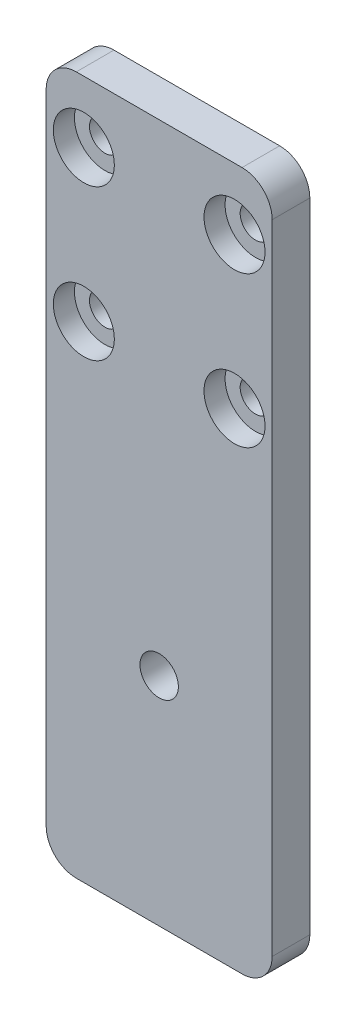
SolidWorks part; units mm, degrees
ref_plane "Alzado" through (0, 0, 0) normal (0, 0, 1) x (1, 0, 0)
ref_plane "Planta" through (0, 0, 0) normal (0, 1, 0) x (1, 0, 0)
ref_plane "Vista lateral" through (0, 0, 0) normal (1, 0, 0) x (0, 0, -1)
sketch "Croquis1" plane through (0, 0, 0) normal (0, 0, 1) x (1, 0, 0)
  line L0 (5, 46.8) -> (25, 66.8) construction
  line L1 (0, 75) -> (30, 75)
  line L2 (0, 75) -> (0, 0)
  line L3 (0, 0) -> (30, 0)
  line L4 (30, 75) -> (30, 0)
  line L5 (15, 56.8) -> (15, 75) construction
  circle A0 centre (5, 66.8) radius 2.05
  circle A1 centre (25, 66.8) radius 2.05
  circle A4 centre (25, 46.8) radius 2.05
  circle A5 centre (5, 46.8) radius 2.05
  circle A6 centre (15, 11.08) radius 2.55
  dimension "D3" = 4.1
  dimension "D11" = 5.1
  dimension "D1" = 30
  dimension "D2" = 75
  dimension "D4" = 20
  dimension "D5" = 63.92
  dimension "D6" = 8.2
  dimension "D7" = 20
extrude "Saliente-Extruir1" add sketch "Croquis1" along normal blind 5
sketch "Croquis4" plane through (0, 0, 5) normal (0, 0, 1) x (1, 0, 0)
  circle A0 centre (5, 66.8) radius 4.05
  circle A1 centre (5, 46.8) radius 4.05
  circle A2 centre (25, 46.8) radius 4.05
  circle A3 centre (25, 66.8) radius 4.05
  dimension "D1" = 8.1
extrude "Cortar-Extruir1" cut sketch "Croquis4" against normal blind 2.8
sketch "Croquis5" plane through (0, 0, 5) normal (0, 0, 1) x (1, 0, 0)
  line L1 (0, 0) -> (30, 0)
  line L2 (0, 0) -> (0, -17.7)
  line L3 (0, -17.7) -> (30, -17.7)
  line L4 (30, 0) -> (30, -17.7)
  dimension "D1" = 17.7
extrude "Saliente-Extruir2" add sketch "Croquis5" against normal through all
fillet "Redondeo1" radius 4 4 edges at (0, 75, 2.5) (30, 75, 2.5) (30, -17.7, 2.5) (0, -17.7, 2.5)
